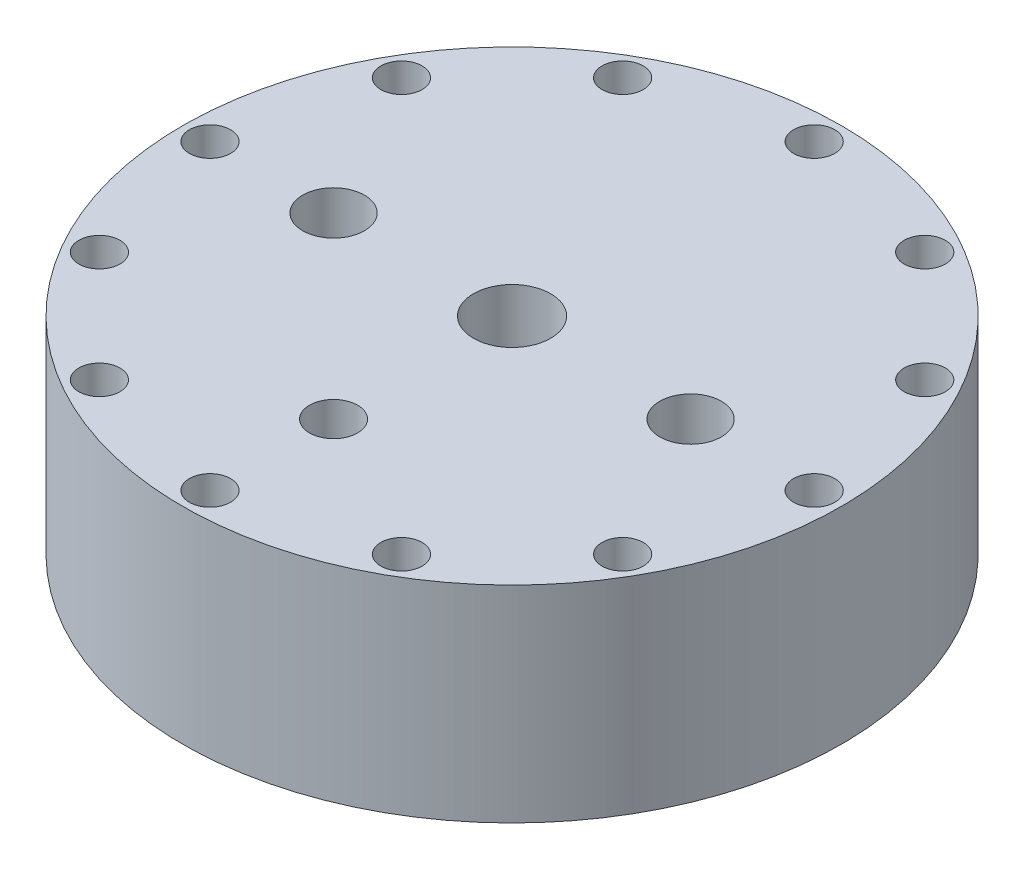
SolidWorks part; units mm, degrees
ref_plane "Front Plane" through (0, 0, 0) normal (0, 0, 1) x (1, 0, 0)
ref_plane "Top Plane" through (0, 0, 0) normal (0, 1, 0) x (1, 0, 0)
ref_plane "Right Plane" through (0, 0, 0) normal (1, 0, 0) x (0, 0, -1)
sketch "Sketch1" plane through (0, 0, 0) normal (0, 0, 1) x (1, 0, 0)
  line L0 (0, 0) -> (-76.2, 0)
  line L1 (-76.2, 0) -> (-76.2, -47.6377)
  line L2 (-76.2, -47.6377) -> (-63.6524, -47.6377)
  line L3 (-57.15, -47.6377) -> (-57.15, -41.2877)
  line L4 (-57.15, -41.2877) -> (-50.8, -41.2877)
  line L5 (-50.8, -41.2877) -> (-50.8, -28.5877)
  line L6 (-50.8, -28.5877) -> (-25.4, -28.5877)
  line L7 (0, -15.8877) -> (0, 0)
  line L8 (-25.4, -28.5877) -> (-25.4, -22.2377)
  line L9 (-12.7, -15.8877) -> (0, -15.8877)
  line L10 (-12.7, -15.8877) -> (-25.4, -22.2377)
  line L11 (-57.15, -47.6377) -> (-59.5884, -47.6377)
  line L12 (-59.5884, -47.6377) -> (-59.5884, -44.9453)
  line L13 (-59.5884, -44.9453) -> (-63.6524, -44.9453)
  line L14 (-63.6524, -44.9453) -> (-63.6524, -47.6377)
  dimension "D1" = 12.7
  dimension "D2" = 76.2
  dimension "D3" = 6.35
  dimension "D4" = 19.05
  dimension "D5" = 6.35
  dimension "D6" = 12.7
  dimension "D7" = 6.35
  dimension "D8" = 25.4
  dimension "D9" = 12.7
  dimension "D10" = 15.8877
  dimension "D11" = 47.6377
  dimension "D12" = 4.064
  dimension "D13" = 2.6924
  dimension "D14" = 63.6524
revolve "Revolve1" add sketch "Sketch1" angle 360 about L7
hole_wizard "3/8 (0.375) Diameter Hole1" positions "Sketch2" profile "Sketch3" hole size "3/8" standard "ANSI Inch"
sketch "Sketch2" plane through (0, 0, 0) normal (0, 1, 0) x (1, 0, 0)
  point P0 (-69.85, 0)
  point P4 (0, 0)
  dimension "D1" = 69.85
sketch "Sketch3" plane through (-69.85, 0, 0) normal (1, 0, 0) x (0, 0, 1)
  line L0 (0, 0) -> (0, 60.0116)
  line L1 (0, 60.0116) -> (4.7625, 57.15)
  line L2 (4.7625, 57.15) -> (4.7625, 0)
  line L5 (4.7625, 0) -> (0, 0)
  line L10 (0, 60.0116) -> (-4.7625, 57.15) construction
  line L11 (0, -6.35) -> (0, 107.95) construction
  dimension "Hole Dia." = 9.525
  dimension "Hole Depth" = 57.15
  dimension "Drill Angle" = 118
pattern_circular "CirPattern1" count 12 over 360 about axis through (0, 0, 0) along (0, 1, 0) of "3/8 (0.375) Diameter Hole1"
hole_wizard "Pipe Tap Drill for 1/2 Tap1" positions "Sketch4" profile "Sketch5" hole size "1/2" standard "ANSI Inch"
sketch "Sketch4" plane through (0, 0, 0) normal (0, 1, 0) x (1, 0, 0)
  point P0 (0, 0)
sketch "Sketch5" plane through (0, 0, 0) normal (1, 0, 0) x (0, 0, 1)
  line L0 (0, 0) -> (0, 24.4145)
  line L1 (0, 24.4145) -> (8.9281, 19.05)
  line L2 (8.9281, 19.05) -> (8.9281, 0)
  line L5 (8.9281, 0) -> (0, 0)
  line L10 (0, 24.4145) -> (-8.9281, 19.05) construction
  line L11 (0, -6.35) -> (0, 107.95) construction
  dimension "Hole Dia." = 17.8562
  dimension "Hole Depth" = 19.05
  dimension "Drill Angle" = 118
hole_wizard "Pipe Tap Drill for 3/8 Tap1" positions "Sketch6" profile "Sketch7" hole size "3/8" standard "ANSI Inch"
sketch "Sketch6" plane through (0, 0, 0) normal (0, 1, 0) x (1, 0, 0)
  point P0 (-41.275, 0)
  point P5 (0, 0)
  dimension "D1" = 41.275
sketch "Sketch7" plane through (-41.275, 0, 0) normal (1, 0, 0) x (0, 0, 1)
  line L0 (0, 0) -> (0, 36.0386)
  line L1 (0, 36.0386) -> (7.1374, 31.75)
  line L2 (7.1374, 31.75) -> (7.1374, 0)
  line L5 (7.1374, 0) -> (0, 0)
  line L10 (0, 36.0386) -> (-7.1374, 31.75) construction
  line L11 (0, -6.35) -> (0, 107.95) construction
  dimension "Hole Dia." = 14.2748
  dimension "Hole Depth" = 31.75
  dimension "Drill Angle" = 118
pattern_circular "CirPattern2" count 2 over 360 about axis through (0, 0, 0) along (0, 1, 0) of "Pipe Tap Drill for 3/8 Tap1"
hole_wizard "Pipe Tap Drill for 1/4 Tap1" positions "Sketch8" profile "Sketch9" hole size "1/4" standard "ANSI Inch"
sketch "Sketch8" plane through (0, 0, 0) normal (0, 1, 0) x (1, 0, 0)
  point P0 (0, -41.275)
  point P4 (0, 0)
  dimension "D1" = 41.275
sketch "Sketch9" plane through (0, 0, 41.275) normal (1, 0, 0) x (0, 0, 1)
  line L0 (0, 0) -> (0, 35.0923)
  line L1 (0, 35.0923) -> (5.5626, 31.75)
  line L2 (5.5626, 31.75) -> (5.5626, 0)
  line L5 (5.5626, 0) -> (0, 0)
  line L10 (0, 35.0923) -> (-5.5626, 31.75) construction
  line L11 (0, -6.35) -> (0, 107.95) construction
  dimension "Hole Dia." = 11.1252
  dimension "Hole Depth" = 31.75
  dimension "Drill Angle" = 118
